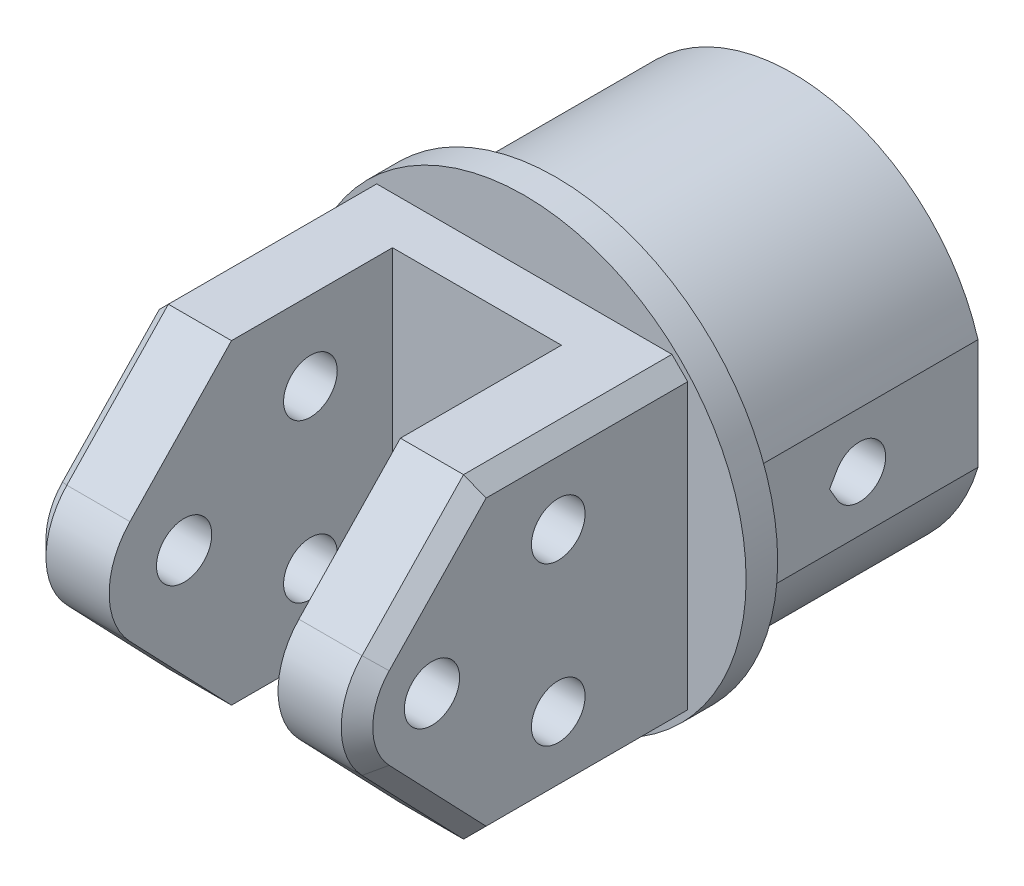
SolidWorks part; units mm, degrees
ref_plane "正面(Front)" through (0, 0, 0) normal (0, 0, 1) x (1, 0, 0)
ref_plane "平面(Top)" through (0, 0, 0) normal (0, 1, 0) x (1, 0, 0)
ref_plane "右側面(Right)" through (0, 0, 0) normal (1, 0, 0) x (0, 0, -1)
sketch "ｽｹｯﾁ1" plane through (0, 0, 0) normal (0, 0, 1) x (1, 0, 0)
  circle A0 centre (0, 0) radius 6.325
  dimension "D1" = 12.65
extrude "ﾎﾞｽ - 押し出し1" add sketch "ｽｹｯﾁ1" against normal blind 15
sketch "ｽｹｯﾁ2" plane through (0, 0, 0) normal (0, 0, 1) x (1, 0, 0)
  line L1 (-10.35, 10) -> (10.35, 10)
  line L2 (-10.35, 10) -> (-10.35, -10)
  line L3 (-10.35, -10) -> (10.35, -10)
  line L4 (10.35, 10) -> (10.35, -10)
  line L5 (-10.35, 10) -> (10.35, -10) construction
  line L6 (-10.35, -10) -> (10.35, 10) construction
  point P0 (0, 0)
  dimension "D1" = 20.7
  dimension "D2" = 20
extrude "ﾎﾞｽ - 押し出し2" add sketch "ｽｹｯﾁ2" along normal blind 5
sketch "ｽｹｯﾁ3" plane through (0, 0, 5) normal (0, 0, 1) x (1, 0, 0)
  line L0 (-10.35, -10) -> (10.35, -10) construction
  line L1 (10.35, 10) -> (5.35, 10)
  line L2 (10.35, 10) -> (10.35, -10)
  line L3 (10.35, -10) -> (5.35, -10)
  line L4 (5.35, 10) -> (5.35, -10)
  line L6 (-10.35, 10) -> (-5.35, 10)
  line L7 (-10.35, 10) -> (-10.35, -10)
  line L8 (-10.35, -10) -> (-5.35, -10)
  line L9 (-5.35, 10) -> (-5.35, -10)
  dimension "D1" = 5
extrude "ﾎﾞｽ - 押し出し3" add sketch "ｽｹｯﾁ3" along normal blind 10.2
fillet "ﾌｨﾚｯﾄ1" [suppressed] radius 5
sketch "ｽｹｯﾁ4" plane through (0, 0, 0) normal (1, 0, 0) x (0, 0, -1)
  line L0 (0, 0) -> (-25.6063, 0) construction
  line L2 (-15.2, -10) -> (-15.2, 10) construction
  circle A0 centre (-10.2, 5) radius 1.7
  circle A1 centre (-10.2, -5) radius 1.7
  dimension "D1" = 3.4
  dimension "D2" = 5
  dimension "D3" = 5
extrude "ｶｯﾄ - 押し出し1" cut sketch "ｽｹｯﾁ4" against normal through all both and the other way through all
sketch "ｽｹｯﾁ5" plane through (0, 0, 0) normal (1, 0, 0) x (0, 0, -1)
  line L0 (0, 0) -> (17.4374, 0) construction
  line L1 (0, -10) -> (0, 10) construction
  circle A0 centre (7.5, 0) radius 1.65
  dimension "D1" = 7.5
  dimension "D2" = 3.3
extrude "ｶｯﾄ - 押し出し2" cut sketch "ｽｹｯﾁ5" against normal through all both and the other way through all
sketch "ｽｹｯﾁ6" plane through (-10.35, 0, 0) normal (-1, 0, 0) x (0, 0, 1)
  line L0 (15.2, 10) -> (21.6305, 3.2854)
  line L1 (0, 0) -> (33.6489, 0) construction
  line L2 (15.2, -10) -> (21.6305, -3.2854)
  line L3 (15.2, -10) -> (15.2, 10)
  arc A0 (21.6305, 3.2854) -> (21.6305, -3.2854) centre (18.2, 0) cw
  circle A1 centre (18.2, 0) radius 1.75
  circle A2 centre (10.2, 5) radius 1.7 construction
  dimension "D1" = 3.5
  dimension "D2" = 8
  dimension "D3" = 3
extrude "ﾎﾞｽ - 押し出し4" add sketch "ｽｹｯﾁ6" against normal blind 5
fillet "ﾌｨﾚｯﾄ2" [suppressed] radius 10
mirror "ﾐﾗｰ1" about plane through (0, 0, 0) normal (1, 0, 0) of "ﾎﾞｽ - 押し出し4", "ﾌｨﾚｯﾄ2"
chamfer "面取り1" [suppressed] distance 1 angle 45
chamfer "面取り2" distance 1 angle 45 10 edges at (10.35, -10, 7.6) (10.35, 10, 7.6) (-10.35, -6.6427, 18.4153) (-10.35, 0, 22.95) (-10.35, 6.6427, 18.4153) (-10.35, 10, 7.6) (-10.35, -10, 7.6) (10.35, -6.6427, 18.4153) (10.35, 0, 22.95) (10.35, 6.6427, 18.4153)
chamfer "面取り3" distance 1 angle 45 1 edges at (6.325, 0, -15)
sketch "ｽｹｯﾁ8" plane through (0, 10, 0) normal (0, 1, 0) x (1, 0, 0)
  line L0 (-16.3251, 0) -> (21.4444, 0)
extrude "ｶｯﾄ - 押し出し3" cut sketch "ｽｹｯﾁ8" against normal through all and the other way through all
sketch "ｽｹｯﾁ9" plane through (0, 0, 0) normal (0, 0, -1) x (-1, 0, 0)
  circle A0 centre (0, 0) radius 9.25
  circle A1 centre (0, 0) radius 12.25
  dimension "D1" = 18.5
  dimension "D2" = 3
extrude "ﾎﾞｽ - 押し出し5" add sketch "ｽｹｯﾁ9" along normal blind 15
sketch "ｽｹｯﾁ10" plane through (0, 0, 0) normal (0, 0, 1) x (1, 0, 0)
  circle A0 centre (0, 0) radius 14.05
  arc A1 (10.35, -6.5529) -> (10.35, 6.5529) centre (0, 0) ccw construction
  dimension "D1" = 1.8
extrude "ﾎﾞｽ - 押し出し6" add sketch "ｽｹｯﾁ10" along normal blind 2
sketch "ｽｹｯﾁ11" plane through (0, 0, 0) normal (1, 0, 0) x (0, 0, -1)
  line L0 (0, -14.05) -> (0, 14.05) construction
  line L1 (0, 0) -> (20.2478, 0) construction
  line L2 (6.0711, 0.825) -> (5.5947, 0)
  line L3 (5.5947, 0) -> (6.0711, -0.825)
  arc A0 (6.0711, -0.825) -> (6.0711, 0.825) centre (7.5, 0) ccw
  dimension "D1" = 7.5
  dimension "D2" = 3.3
  dimension "D3" = 60
extrude "ｶｯﾄ - 押し出し4" cut sketch "ｽｹｯﾁ11" against normal through all both and the other way through all
sketch "ｽｹｯﾁ12" plane through (0, 0, -15) normal (0, 0, -1) x (-1, 0, 0)
  line L0 (-11.7394, 3.5) -> (-11.7394, -3.5)
  line L1 (0, 0) -> (0, 22.0096) construction
  line L2 (11.7394, 3.5) -> (11.7394, -3.5)
  line L3 (-11.7394, 3.5) -> (-16.1799, 3.5)
  line L4 (-16.1799, 3.5) -> (-16.1799, -3.5)
  line L5 (-16.1799, -3.5) -> (-11.7394, -3.5)
  line L6 (11.7394, -3.5) -> (17.2092, -3.5)
  line L7 (17.2092, -3.5) -> (17.2092, 3.5)
  line L8 (17.2092, 3.5) -> (11.7394, 3.5)
  circle A0 centre (0, 0) radius 12.25 construction
  dimension "D1" = 7
extrude "ｶｯﾄ - 押し出し5" cut sketch "ｽｹｯﾁ12" against normal up to surface (15 mm away) up to face at (-12.25, 0, 0)
